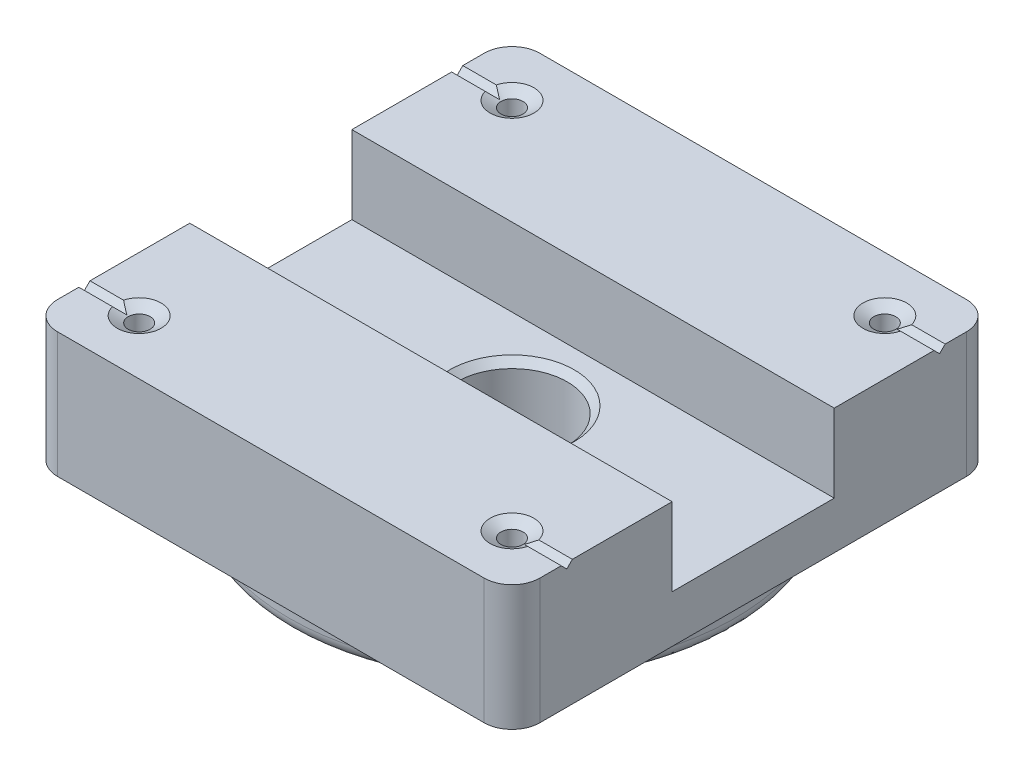
SolidWorks part; units mm, degrees
material "6061-T6 Al"
ref_plane "Front Plane" through (0, 0, 0) normal (0, 0, 1) x (1, 0, 0)
ref_plane "Top Plane" through (0, 0, 0) normal (0, 1, 0) x (1, 0, 0)
ref_plane "Right Plane" through (0, 0, 0) normal (1, 0, 0) x (0, 0, -1)
sketch "Sketch1" plane through (0, 0, 0) normal (0, 1, 0) x (1, 0, 0)
  line L0 (21.9964, 21.9964) -> (-21.9964, -21.9964) construction
  line L1 (-21.9964, 21.9964) -> (21.9964, 21.9964)
  line L2 (-21.9964, 21.9964) -> (-21.9964, -21.9964)
  line L3 (-21.9964, -21.9964) -> (21.9964, -21.9964)
  line L4 (21.9964, 21.9964) -> (21.9964, -21.9964)
  point P4 (0, 0)
  dimension "D1" = 43.9928
extrude "Extrude1" add sketch "Sketch1" along normal blind 11.43
hole_wizard "M2x0.4 Tapped Hole1" positions "Sketch3" profile "Sketch2" tap size "M2x0.4" standard "Ansi Metric" end condition through all
sketch "Sketch3" plane through (-12.6968, 11.43, 8.7351) normal (0, -1, 0) x (1, 0, 0)
  line L0 (-4.3032, -25.7351) -> (29.6968, -25.7351) construction
  line L1 (29.6968, -25.7351) -> (29.6968, 8.2649) construction
  line L2 (29.6968, 8.2649) -> (-4.3032, 8.2649) construction
  line L3 (-4.3032, 8.2649) -> (29.6968, -25.7351) construction
  point P0 (-4.3032, -25.7351)
  point P1 (-4.3032, 8.2649)
  point P3 (29.6968, 8.2649)
  point P5 (29.6968, -25.7351)
  point P14 (12.6968, -8.7351)
  dimension "D1" = 34
sketch "Sketch2" plane through (-17, 11.43, -17) normal (1, 0, 0) x (0, 0, 1)
  line L0 (0, 0) -> (0, 11.43)
  line L1 (0, 11.43) -> (0.8, 11.43)
  line L3 (0.8, 11.43) -> (0.8, 8.001)
  line L4 (1, 8.001) -> (0.8, 8.001)
  line L5 (1, 8.001) -> (1, 0.5774)
  line L6 (1, 0.5774) -> (2, 0)
  line L7 (2, 0) -> (0, 0)
  line L8 (-1, 0.5774) -> (-2, 0) construction
  line L11 (0, -6.35) -> (0, 107.95) construction
  dimension "Thru Tap Drill Dia." = 1.6
  dimension "Thru Tap Drill Depth" = 11.43
  dimension "Thread Major Dia." = 2
  dimension "Thread Depth" = 8.001
  dimension "Near C'Sink Dia." = 4
  dimension "Near C'Sink Angle" = 120
fillet "Fillet1" radius 2.54 4 edges at (-21.9964, 5.715, -21.9964) (21.9964, 5.715, -21.9964) (21.9964, 5.715, 21.9964) (-21.9964, 5.715, 21.9964)
sketch "Sketch5" plane through (0, 0, 0) normal (1, 0, 0) x (0, 0, -1)
  line L0 (0, 0) -> (0, -19.6341) construction
  line L1 (-20.32, -3.019) -> (-20.32, 0)
  line L3 (-20.32, 0) -> (0, 0)
  line L4 (-19.4564, 11.43) -> (19.4564, 11.43) construction
  line L5 (-19.4564, 11.43) -> (19.4564, 11.43) construction
  line L6 (0, -19.6341) -> (0, -16.5506) construction
  line L7 (-8.6155, -7.9031) -> (0, -7.9031)
  line L8 (-21.9964, 0) -> (-19.4564, 0) construction
  line L9 (-21.9964, 0) -> (-19.4564, 0) construction
  line L10 (0, 0) -> (0, 29.21) construction
  line L12 (0, -7.9031) -> (0, 0)
  arc A0 (-27.1684, -13.3766) -> (-6.35, -20.9041) centre (0, 29.21) ccw construction
  arc A2 (-20.32, -3.019) -> (-8.6155, -7.9031) centre (0, 29.21) ccw
  dimension "D6" = 76.2
  dimension "D1" = 17.78
  dimension "D2" = 40.64
  dimension "D4" = 1.6764
  dimension "D5" = 12.7
revolve "Revolve2" add sketch "Sketch5" angle 360 about L6
fillet "Fillet2" radius 0.762 1 edges at (0, 0, 20.32)
fillet "Fillet3" radius 1.27 1 edges at (0, -3.019, -20.32)
sketch "Sketch8" plane through (0, 11.43, 0) normal (0, 1, 0) x (1, 0, 0)
  line L0 (-21.9964, 19.4564) -> (-21.9964, -19.4564) construction
  line L1 (-21.9964, 7.3914) -> (21.9964, 7.3914)
  line L2 (-21.9964, 7.3914) -> (-21.9964, -7.3914)
  line L3 (-21.9964, -7.3914) -> (21.9964, -7.3914)
  line L4 (21.9964, 7.3914) -> (21.9964, -7.3914)
  line L5 (21.9964, -19.4564) -> (21.9964, 19.4564) construction
  line L6 (0, 0) -> (21.9964, 0) construction
  dimension "D1" = 14.7828
extrude "Cut-Extrude1" cut sketch "Sketch8" against normal blind 7.112
hole_wizard "3/8 Clearance Hole1" positions "Sketch7" profile "Sketch6" hole size "3/8" standard "Ansi Inch" end condition through all
sketch "Sketch7" plane through (-2.6974, 4.318, -0.912) normal (0, 1, 0) x (-1, 0, 0)
  point P1 (-2.6974, 0.912)
sketch "Sketch6" plane through (0, 4.318, 0) normal (1, 0, 0) x (0, 0, 1)
  line L0 (0, 0) -> (0, 12.2211)
  line L1 (0, 12.2211) -> (5.0419, 12.2211)
  line L2 (5.0419, 12.2211) -> (5.0419, 0.635)
  line L3 (5.0419, 0.635) -> (5.6769, 0)
  line L5 (5.6769, 0) -> (0, 0)
  line L6 (-5.0419, 0.635) -> (-5.6769, 0) construction
  line L11 (0, -6.35) -> (0, 107.95) construction
  dimension "Thru Hole Dia." = 10.0838
  dimension "Thru Hole Depth" = 12.2211
  dimension "Near C'Sink Dia." = 11.3538
  dimension "Near C'Sink Angle" = 90
sketch "Sketch9" plane through (-21.9964, 0, 0) normal (-1, 0, 0) x (0, 0, 1)
  line L0 (-17.508, 11.43) -> (-17, 10.922)
  line L1 (-19.4564, 11.43) -> (-7.3914, 11.43) construction
  line L2 (-17, 10.922) -> (-16.492, 11.43)
  line L3 (-16.492, 11.43) -> (-17.508, 11.43)
  line L4 (16.492, 11.43) -> (17, 10.922)
  line L5 (7.3914, 11.43) -> (19.4564, 11.43) construction
  line L6 (17, 10.922) -> (17.508, 11.43)
  line L7 (17.508, 11.43) -> (16.492, 11.43)
  point P9 (-17, 11.43)
  point P11 (17, 11.43)
  dimension "D1" = 0.508
extrude "Cut-Extrude2" cut sketch "Sketch9" against normal up to vertex (4.9964 mm away) up to point (-17, 11.43, -17)
mirror "Mirror1" about plane through (0, 0, 0) normal (1, 0, 0) of "Cut-Extrude2"
fillet "Fillet4" radius 2.54 1 edges at (0, -7.9031, -8.6155)
